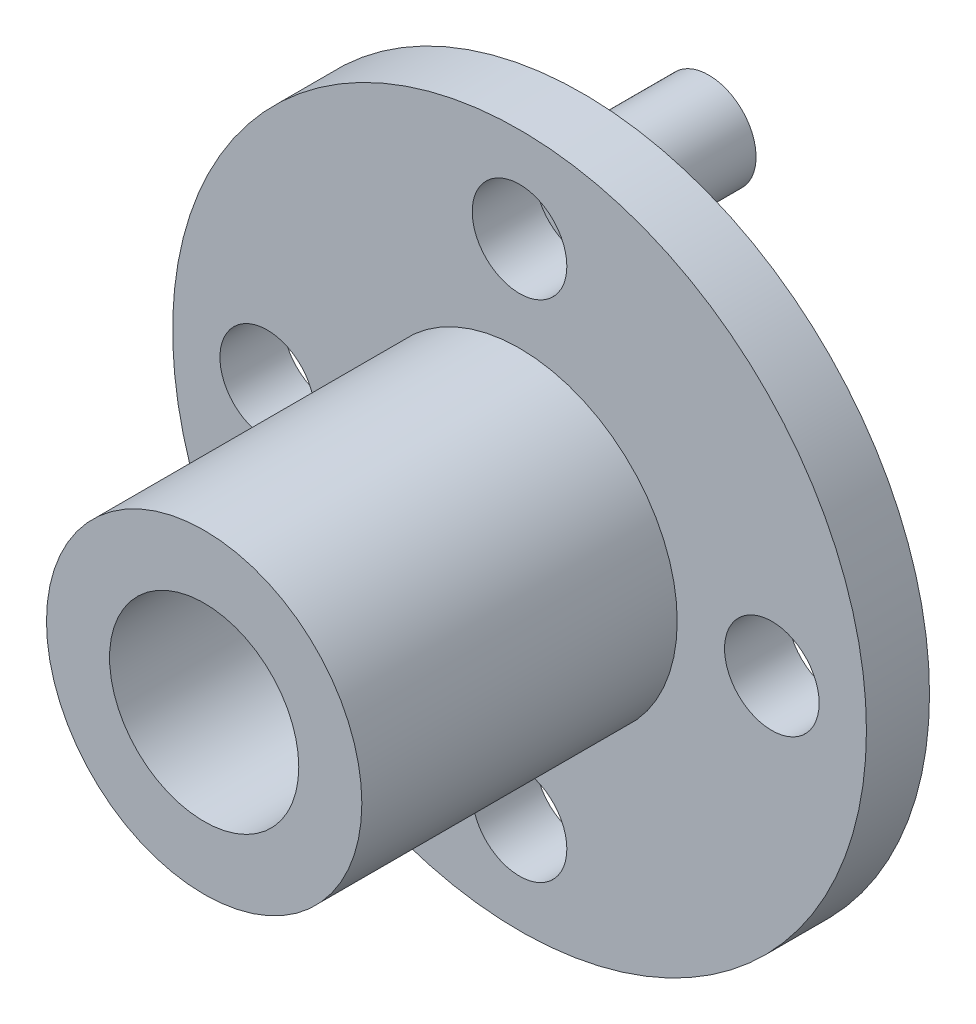
SolidWorks part; units mm, degrees
ref_plane "前视基准面" through (0, 0, 0) normal (0, 0, 1) x (1, 0, 0)
ref_plane "上视基准面" through (0, 0, 0) normal (0, 1, 0) x (1, 0, 0)
ref_plane "右视基准面" through (0, 0, 0) normal (1, 0, 0) x (0, 0, -1)
sketch "草图1" plane through (0, 0, 0) normal (0, 0, 1) x (1, 0, 0)
  circle A0 centre (0, 0) radius 11
  dimension "D1" = 22
extrude "凸台-拉伸1" add sketch "草图1" along normal blind 2
sketch "草图2" plane through (0, 0, 2) normal (0, 0, 1) x (1, 0, 0)
  circle A0 centre (0, 0) radius 5
  dimension "D1" = 10
extrude "凸台-拉伸2" add sketch "草图2" along normal blind 10
sketch "草图4" plane through (0, 0, 12) normal (0, 0, 1) x (1, 0, 0)
  circle A0 centre (0, 0) radius 3
  dimension "D1" = 6
extrude "切除-拉伸2" cut sketch "草图4" against normal through all
sketch "草图5" plane through (0, 0, 2) normal (0, 0, 1) x (1, 0, 0)
  circle A1 centre (-8, 0) radius 1.5
  circle A2 centre (0, 8) radius 1.5
  circle A3 centre (8, 0) radius 1.5
  circle A4 centre (0, -8) radius 1.5
  point P13 (0, 0)
  dimension "D1" = 16
  dimension "D2" = 3
  dimension "D3" = 4
extrude "切除-拉伸3" cut sketch "草图5" against normal up to next
sketch "草图6" plane through (0, 0, 0) normal (0, 0, -1) x (-1, 0, 0)
  circle A0 centre (0, 8) radius 1.5
  dimension "D1" = 3
extrude "凸台-拉伸3" add sketch "草图6" along normal blind 4 separate body
